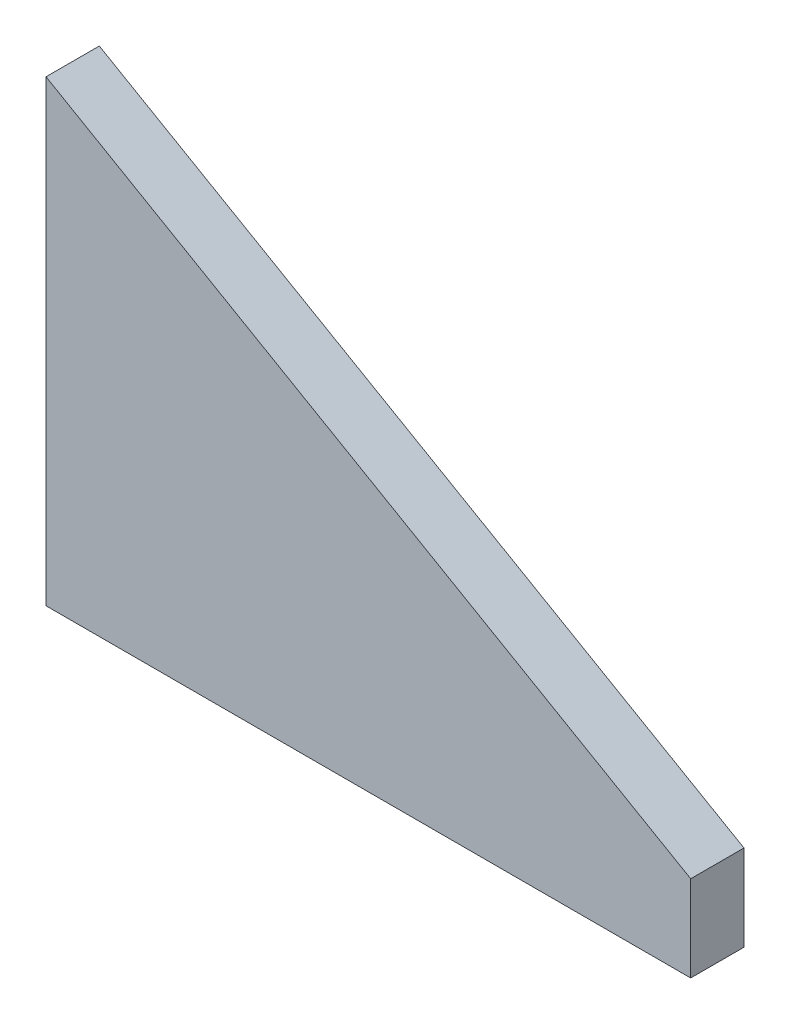
SolidWorks part; units mm, degrees
ref_plane "Front Plane" through (0, 0, 0) normal (0, 0, 1) x (1, 0, 0)
ref_plane "Top Plane" through (0, 0, 0) normal (0, 1, 0) x (1, 0, 0)
ref_plane "Right Plane" through (0, 0, 0) normal (1, 0, 0) x (0, 0, -1)
sketch "Sketch1" plane through (0, 0, 0) normal (0, 0, 1) x (1, 0, 0)
  line L0 (-9.525, 4.0132) -> (9.525, -6.985)
  line L1 (-9.525, -9.525) -> (9.525, -9.525)
  line L2 (-9.525, -9.525) -> (-9.525, -6.985)
  line L3 (9.525, -9.525) -> (9.525, -6.985)
  line L4 (-9.525, -6.985) -> (-9.525, 4.0132)
  point P0 (0, 0)
extrude "Extrude1" add sketch "Sketch1" along normal mid plane 1.5748
sketch "Sketch2" plane through (0, -9.525, 0) normal (0, -1, 0) x (1, 0, 0)
  line L0 (0, 0.7874) -> (0, -0.7874) construction
  line L1 (-9.525, 0.7874) -> (9.525, 0.7874) construction
  line L2 (-9.525, -0.7874) -> (9.525, -0.7874) construction
